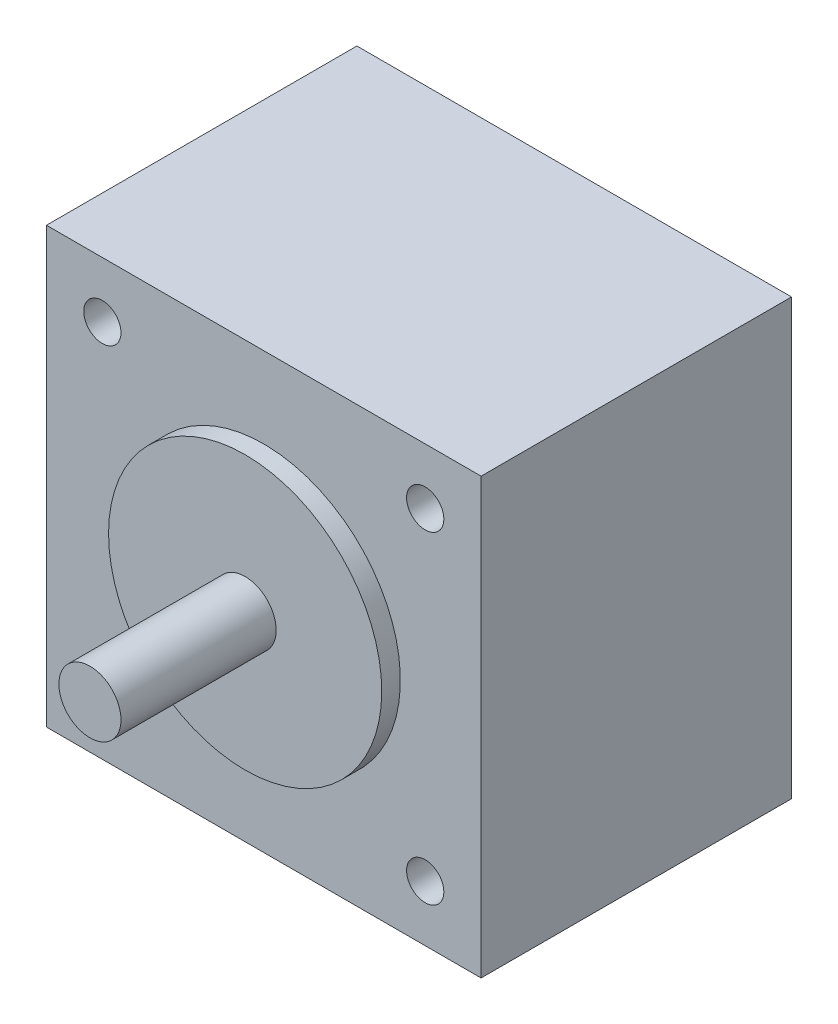
SolidWorks part; units mm, degrees
ref_plane "Front Plane" through (0, 0, 0) normal (0, 0, 1) x (1, 0, 0)
ref_plane "Top Plane" through (0, 0, 0) normal (0, 1, 0) x (1, 0, 0)
ref_plane "Right Plane" through (0, 0, 0) normal (1, 0, 0) x (0, 0, -1)
sketch "Sketch1" plane through (0, 0, 0) normal (0, 0, 1) x (1, 0, 0)
  line L1 (-17.5, -17.5) -> (17.5, -17.5)
  line L2 (-17.5, -17.5) -> (-17.5, 17.5)
  line L3 (-17.5, 17.5) -> (17.5, 17.5)
  line L4 (17.5, -17.5) -> (17.5, 17.5)
  line L5 (-17.5, -17.5) -> (17.5, 17.5) construction
  line L6 (-17.5, 17.5) -> (17.5, -17.5) construction
  line L7 (-13, -13) -> (13, -13) construction
  line L8 (-13, -13) -> (-13, 13) construction
  line L9 (-13, 13) -> (13, 13) construction
  line L10 (13, -13) -> (13, 13) construction
  line L11 (-13, -13) -> (13, 13) construction
  line L12 (-13, 13) -> (13, -13) construction
  circle A0 centre (-13, 13) radius 1.5
  circle A1 centre (13, 13) radius 1.5
  circle A2 centre (-13, -13) radius 1.5
  circle A3 centre (13, -13) radius 1.5
  point P0 (0, 0)
  point P6 (0, 0)
extrude "Boss-Extrude1" add sketch "Sketch1" along normal blind 25
sketch "Sketch2" plane through (0, 0, 25) normal (0, 0, 1) x (1, 0, 0)
  circle A0 centre (0, 0) radius 11
extrude "Boss-Extrude2" add sketch "Sketch2" along normal blind 1.5
sketch "Sketch3" plane through (0, 0, 26.5) normal (0, 0, 1) x (1, 0, 0)
  circle A0 centre (0, 0) radius 2.5
extrude "Boss-Extrude3" add sketch "Sketch3" along normal blind 12.5
sketch "Sketch4" plane through (0, 0, 0) normal (0, 0, -1) x (-1, 0, 0)
  circle A0 centre (0, 0) radius 2.5
extrude "Boss-Extrude4" add sketch "Sketch4" along normal blind 10
